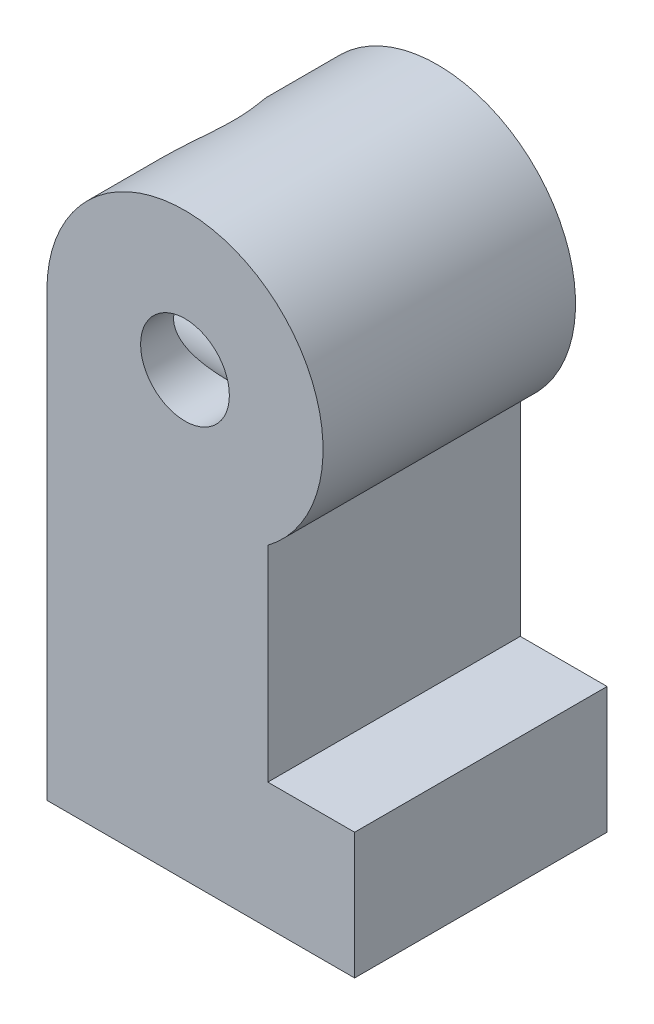
SolidWorks part; units mm, degrees
ref_plane "Front Plane" through (0, 0, 0) normal (0, 0, 1) x (1, 0, 0)
ref_plane "Top Plane" through (0, 0, 0) normal (0, 1, 0) x (1, 0, 0)
ref_plane "Right Plane" through (0, 0, 0) normal (1, 0, 0) x (0, 0, -1)
sketch "Sketch1" plane through (0, 0, 0) normal (0, 0, 1) x (1, 0, 0)
  line L0 (-3.5, 0) -> (-3.5, -11.2)
  line L1 (-3.5, -11.2) -> (4.3, -11.2)
  line L2 (4.3, -11.2) -> (4.3, -8)
  line L3 (4.3, -8) -> (2.1, -8)
  line L4 (2.1, -8) -> (2.1, -2.8)
  circle A0 centre (0, 0) radius 1.125
  arc A1 (2.1, -2.8) -> (-3.5, 0) centre (0, 0) ccw
  dimension "D1" = 2.25
  dimension "D2" = 7
  dimension "D3" = 11.2
  dimension "D4" = 3.2
  dimension "D5" = 7.8
  dimension "D6" = 5.6
extrude "Boss-Extrude1" add sketch "Sketch1" along normal mid plane 6.4
sketch "Sketch2" plane through (0, -11.2, 0) normal (0, -1, 0) x (1, 0, 0)
  line L0 (-3.5, 3.2) -> (-3.5, -3.2) construction
  line L1 (-2.1, 2.4) -> (1.2, 2.4)
  line L2 (-2.1, 2.4) -> (-2.1, -2.4)
  line L3 (-2.1, -2.4) -> (1.2, -2.4)
  line L4 (1.2, 2.4) -> (1.2, -2.4)
  line L5 (-3.5, -3.2) -> (4.3, -3.2) construction
  dimension "D1" = 3.3
  dimension "D2" = 4.8
  dimension "D3" = 1.4
  dimension "D4" = 0.8
extrude "Cut-Extrude1" cut sketch "Sketch2" against normal blind 8.9
sketch "Sketch4" plane through (-3.5, 0, 0) normal (-1, 0, 0) x (0, 0, 1)
  line L1 (3.2, -11.2) -> (-3.2, -11.2) construction
  line L2 (-3.2, 3.5) -> (-3.2, -2.8) construction
  circle A0 centre (0, 0.5) radius 2.4
  dimension "D1" = 4.8
  dimension "D2" = 11.7
  dimension "D3" = 3.2
extrude "Cut-Extrude2" cut sketch "Sketch4" against normal blind 5
